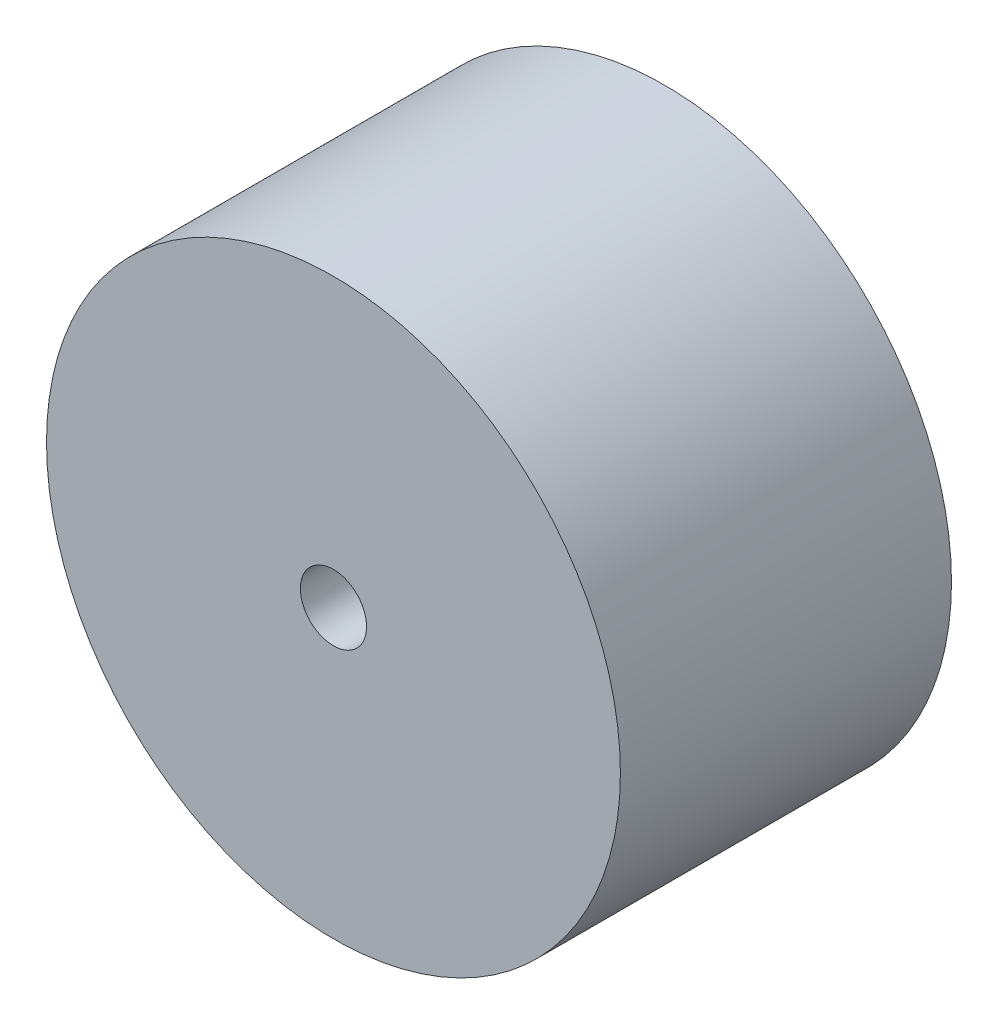
SolidWorks part; units mm, degrees
ref_plane "Front Plane" through (0, 0, 0) normal (0, 0, 1) x (1, 0, 0)
ref_plane "Top Plane" through (0, 0, 0) normal (0, 1, 0) x (1, 0, 0)
ref_plane "Right Plane" through (0, 0, 0) normal (1, 0, 0) x (0, 0, -1)
sketch "Sketch1" plane through (0, 0, 0) normal (0, 0, 1) x (1, 0, 0)
  circle A0 centre (0, 0) radius 26
  circle A1 centre (0, 0) radius 22.5
  circle A2 centre (0, 0) radius 3
  dimension "D1" = 6
  dimension "D2" = 52
  dimension "D3" = 45
extrude "Boss-Extrude1" add sketch "Sketch1" along normal blind 30 contours A1 A2 | A0 A1
